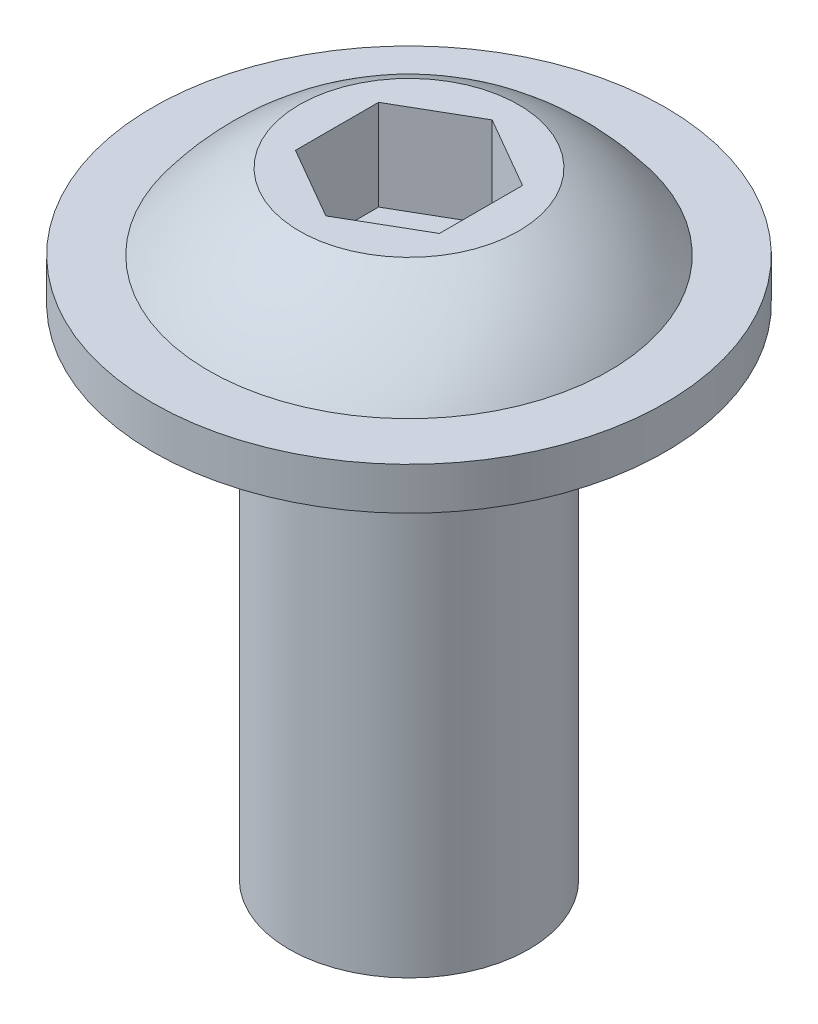
SolidWorks part; units mm, degrees
ref_plane "Front Plane" through (0, 0, 0) normal (0, 0, 1) x (1, 0, 0)
ref_plane "Top Plane" through (0, 0, 0) normal (0, 1, 0) x (1, 0, 0)
ref_plane "Right Plane" through (0, 0, 0) normal (1, 0, 0) x (0, 0, -1)
sketch "Sketch1" plane through (0, 0, 0) normal (0, 1, 0) x (1, 0, 0)
  circle A0 centre (0, 0) radius 3.9688
  dimension "D1" = 7.9375
extrude "Boss-Extrude1" add sketch "Sketch1" along normal blind 16.5
sketch "Sketch2" plane through (0, 16.5, 0) normal (0, 1, 0) x (1, 0, 0)
  circle A0 centre (0, 0) radius 8.475
  dimension "D1" = 16.95
extrude "Boss-Extrude2" add sketch "Sketch2" along normal blind 1.4
sketch "Sketch3" plane through (0, 0, 0) normal (0, 0, 1) x (1, 0, 0)
  line L0 (8.475, 17.9) -> (-8.475, 17.9) construction
  line L1 (8.475, 17.9) -> (6.625, 17.9) construction
  line L2 (-3.625, 20.4) -> (0, 20.4)
  line L3 (0, 20.4) -> (0, 17.9) construction
  line L4 (-6.625, 17.9) -> (0, 17.9)
  line L5 (0, 17.9) -> (-8.475, 17.9) construction
  line L6 (0, 20.4) -> (0, 17.9)
  arc A0 (-6.625, 17.9) -> (-3.625, 20.4) centre (0, 13) cw
  dimension "D4" = 8.2402
  dimension "D1" = 13.25
  dimension "D2" = 2.5
  dimension "D3" = 3.625
  dimension "D5" = 6.625
revolve "Revolve2" add sketch "Sketch3" angle 360 about L3
sketch "Sketch4" plane through (0, 20.4, 0) normal (0, 1, 0) x (1, 0, 0)
  line L1 (-2.3813, 1.3748) -> (-2.3813, -1.3748)
  line L2 (-2.3813, -1.3748) -> (0, -2.7496)
  line L3 (0, -2.7496) -> (2.3813, -1.3748)
  line L4 (2.3813, -1.3748) -> (2.3813, 1.3748)
  line L5 (2.3813, 1.3748) -> (0, 2.7496)
  line L6 (0, 2.7496) -> (-2.3813, 1.3748)
  circle A0 centre (0, 0) radius 2.3813 construction
  dimension "D1" = 4.7625
extrude "Cut-Extrude1" cut sketch "Sketch4" against normal blind 3
